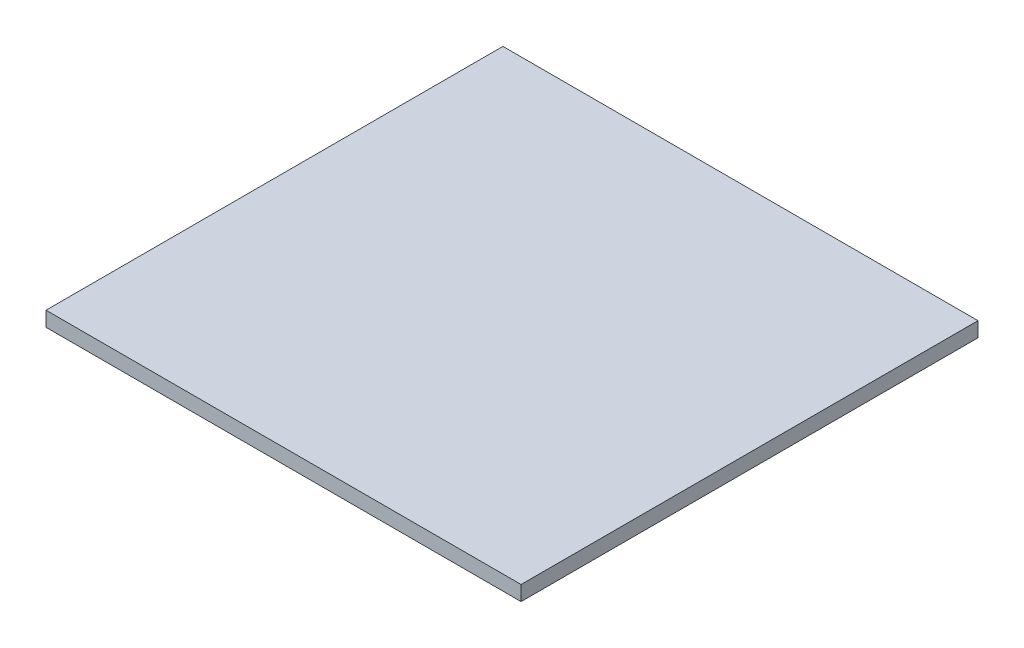
SolidWorks part; units mm, degrees
ref_plane "Спереди" through (0, 0, 0) normal (0, 0, 1) x (1, 0, 0)
ref_plane "Сверху" through (0, 0, 0) normal (0, 1, 0) x (1, 0, 0)
ref_plane "Справа" through (0, 0, 0) normal (1, 0, 0) x (0, 0, -1)
sketch "Эскиз1" plane through (0, 0, 0) normal (0, 1, 0) x (1, 0, 0)
  line L1 (288, -277) -> (-288, -277)
  line L2 (288, -277) -> (288, 277)
  line L3 (288, 277) -> (-288, 277)
  line L4 (-288, -277) -> (-288, 277)
  line L5 (288, -277) -> (-288, 277) construction
  line L6 (288, 277) -> (-288, -277) construction
  point P0 (0, 0)
  dimension "D1" = 576
  dimension "D2" = 554
extrude "Бобышка-Вытянуть1" add sketch "Эскиз1" along normal blind 18
